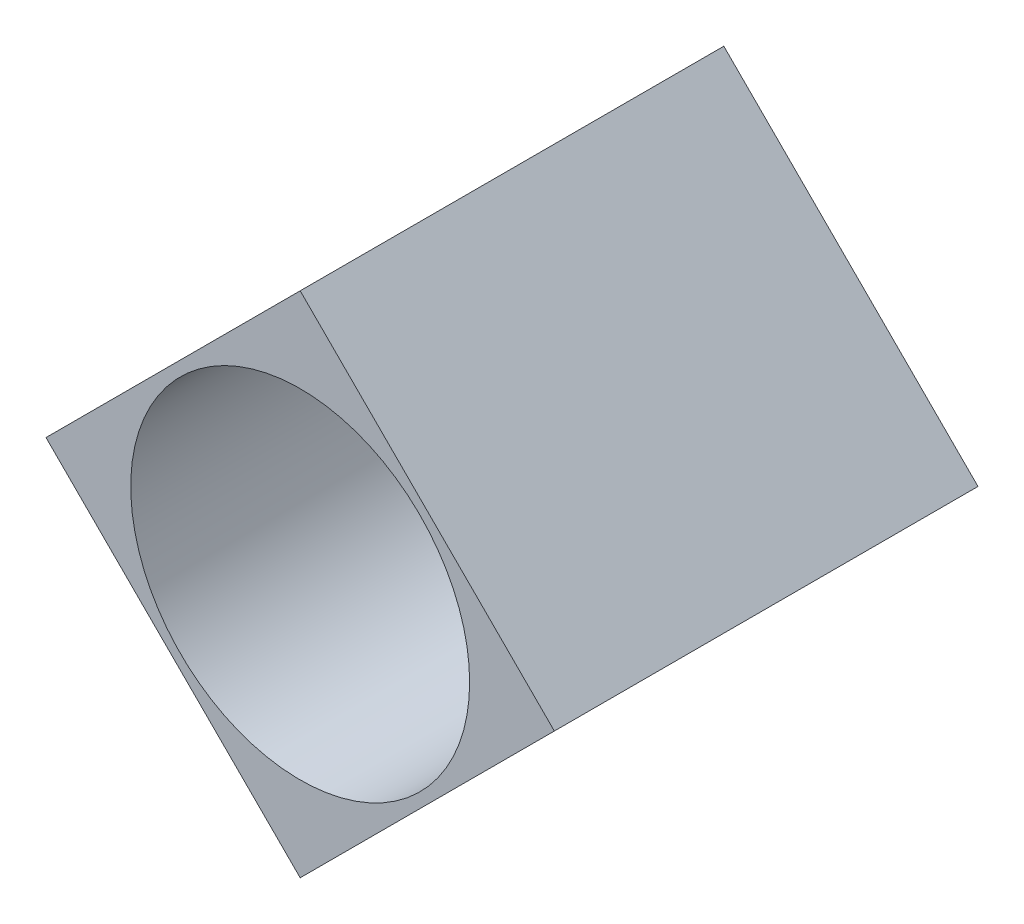
SolidWorks part; units mm, degrees
material "Hierro dúctil"
ref_plane "Alzado" through (0, 0, 0) normal (0, 0, 1) x (1, 0, 0)
ref_plane "Planta" through (0, 0, 0) normal (0, 1, 0) x (1, 0, 0)
ref_plane "Vista lateral" through (0, 0, 0) normal (1, 0, 0) x (0, 0, -1)
sketch "Croquis1" plane through (0, 0, 0) normal (0, 0, 1) x (1, 0, 0)
  line L0 (0, 3) -> (3, 0)
  line L1 (3, 0) -> (0, -3)
  line L2 (0, -3) -> (-3, 0)
  line L3 (-3, 0) -> (0, 3)
  circle A0 centre (0, 0) radius 2
  dimension "D1" = 4
extrude "Saliente-Extruir1" add sketch "Croquis1" along normal blind 5
